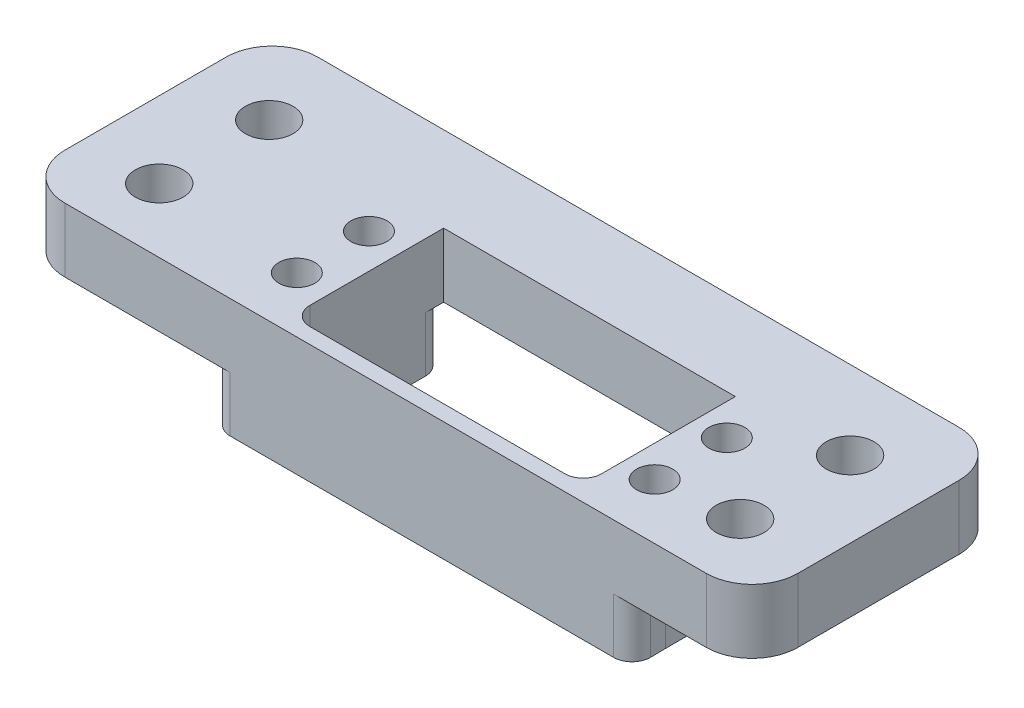
SolidWorks part; units mm, degrees
ref_plane "Front Plane" through (0, 0, 0) normal (0, 0, 1) x (1, 0, 0)
ref_plane "Top Plane" through (0, 0, 0) normal (0, 1, 0) x (1, 0, 0)
ref_plane "Right Plane" through (0, 0, 0) normal (1, 0, 0) x (0, 0, -1)
sketch "Sketch1" plane through (0, 0, 0) normal (0, 1, 0) x (1, 0, 0)
  line L1 (0, 0) -> (101.6, 0)
  line L2 (0, 0) -> (0, 35.052)
  line L3 (0, 35.052) -> (101.6, 35.052)
  line L4 (101.6, 0) -> (101.6, 35.052)
  dimension "1.38" = 35.052
  dimension "D2" = 101.6
extrude "Initial Extrude" add sketch "Sketch1" along normal blind 8.89 contours L2 L3 L4 L1
sketch "Sketch2" plane through (0, 8.89, 0) normal (0, 1, 0) x (1, 0, 0)
  line L0 (0, 0) -> (101.6, 0) construction
  line L1 (0, 0) -> (0, 35.052) construction
  line L2 (101.6, 0) -> (101.6, 35.052) construction
  circle A0 centre (10.541, 24.13) radius 3.302
  circle A1 centre (10.541, 8.89) radius 3.302
  circle A2 centre (91.059, 24.13) radius 3.302
  circle A3 centre (91.059, 8.89) radius 3.302
  dimension "D1" = 6.604
  dimension "D2" = 15.24
  dimension "D3" = 8.89
  dimension "D4" = 80.518
  dimension "D5" = 10.541
  dimension "D6" = 10.541
extrude "Screw Holes" cut sketch "Sketch2" against normal through all contours A1 | A2 | A0 | A3
sketch "Sketch4" plane through (0, 8.89, 0) normal (0, 1, 0) x (1, 0, 0)
  line L0 (30.8, 17.7) -> (30.8, 7.7)
  line L1 (35.6087, 23.241) -> (76.041, 23.241)
  line L2 (35.6087, 23.241) -> (35.6087, 2.159)
  line L3 (35.6087, 2.159) -> (76.041, 2.159)
  line L4 (76.041, 23.241) -> (76.041, 2.159)
  line L5 (101.6, 0) -> (101.6, 35.052) construction
  line L7 (0, 0) -> (101.6, 0) construction
  circle A3 centre (65.5, 12.7) radius 10.541
  circle A4 centre (30.8, 17.7) radius 2.5
  circle A5 centre (30.8, 7.7) radius 2.5
  circle A6 centre (80.4, 17.7) radius 2.5
  circle A7 centre (80.4, 7.7) radius 2.5
  point P4 (35.6087, 12.7)
  point P20 (30.8, 12.7)
  dimension "D1" = 5
  dimension "D2" = 10
  dimension "D4" = 21.082
  dimension "D5" = 49.6
  dimension "D6" = 12.7
  dimension "D7" = 36.1
  dimension "D8" = 14.9
extrude "Servo Hole" cut sketch "Sketch4" against normal through all
fillet "Fillet1" radius 6.35 4 edges at (101.6, 4.445, -35.052) (101.6, 4.445, 0) (0, 4.445, 0) (0, 4.445, -35.052)
sketch "Sketch6" plane through (0, 0, 0) normal (0, -1, 0) x (-1, 0, 0)
  circle A0 centre (-10.541, 8.89) radius 5.715
  circle A1 centre (-10.541, 24.13) radius 5.715
  circle A2 centre (-91.059, 24.13) radius 5.715
  circle A3 centre (-91.059, 8.89) radius 5.715
  circle A4 centre (-10.541, 24.13) radius 3.302 construction
  circle A6 centre (-91.059, 24.13) radius 3.302 construction
  circle A7 centre (-91.059, 8.89) radius 3.302 construction
  dimension "D1" = 11.43
extrude "Screw Head Hole" cut sketch "Sketch6" against normal blind 3.81
sketch "Sketch7" plane through (0, 0, 0) normal (0, -1, 0) x (1, 0, 0)
  line L0 (35.6087, -23.241) -> (76.041, -23.241) construction
  line L1 (35.6087, -2.159) -> (26.7187, -2.159)
  line L2 (35.6087, -2.159) -> (35.6087, -23.241)
  line L3 (35.6087, -23.241) -> (26.7187, -23.241)
  line L4 (26.7187, -2.159) -> (26.7187, -23.241)
  line L5 (76.041, -2.159) -> (84.931, -2.159)
  line L6 (76.041, -2.159) -> (76.041, -23.241)
  line L7 (76.041, -23.241) -> (84.931, -23.241)
  line L8 (84.931, -2.159) -> (84.931, -23.241)
  circle A20 centre (30.8, -7.7) radius 2.55
  circle A21 centre (30.8, -17.7) radius 2.55
  circle A22 centre (80.4, -7.7) radius 2.55
  circle A23 centre (80.4, -17.7) radius 2.55
  dimension "D1" = 8.89
  dimension "D2" = 8.89
extrude "Boss-Extrude1" add sketch "Sketch7" along normal blind 7.62 contours L1 L4 L3 L2
fillet "Fillet2" radius 2.54 8 edges at (35.6087, -3.81, -23.241) (76.041, -3.81, -23.241) (84.931, -3.81, -23.241) (26.7187, -3.81, -23.241) (76.041, -3.81, -2.159) (35.6087, -3.81, -2.159) (84.931, -3.81, -2.159) (26.7187, -3.81, -2.159)
sketch "Sketch8" plane through (0, 0, 0) normal (0, -1, 0) x (1, 0, 0)
  line L0 (26.7187, -4.699) -> (26.7187, 0)
  line L1 (6.35, 0) -> (95.25, 0) construction
  line L2 (26.7187, 0) -> (84.9973, 0)
  line L3 (84.9973, 0) -> (84.931, -4.699)
  line L4 (84.931, -20.701) -> (84.931, -4.699) construction
  line L5 (26.7187, -4.699) -> (35.6087, -4.699)
  line L6 (35.6087, -20.701) -> (35.6087, -4.699) construction
  line L7 (35.6087, -4.699) -> (35.6087, -2.159)
  line L8 (35.6087, -2.159) -> (76.041, -2.159)
  line L9 (76.041, -2.159) -> (76.041, -4.699)
  line L10 (76.041, -4.699) -> (84.931, -4.699)
  point P5 (84.931, -5.0815)
extrude "Boss-Extrude2" add sketch "Sketch8" along normal up to surface (7.62 mm away) up to face at (31.1637, -7.62, -12.7)
fillet "Fillet3" radius 2.54 4 edges at (84.9973, -3.81, 0) (26.7187, -3.81, 0) (76.041, 0.635, -2.159) (35.6087, 0.635, -2.159)
